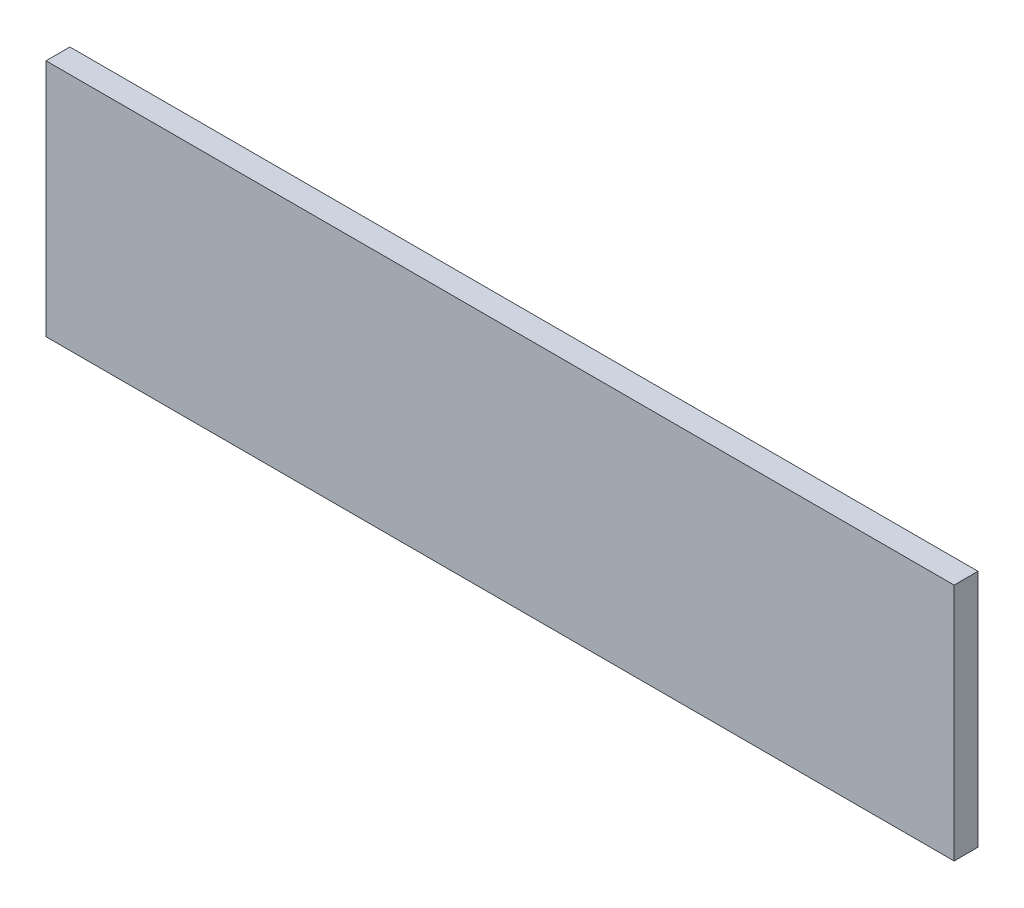
SolidWorks part; units mm, degrees
ref_plane "Front Plane" through (0, 0, 0) normal (0, 0, 1) x (1, 0, 0)
ref_plane "Top Plane" through (0, 0, 0) normal (0, 1, 0) x (1, 0, 0)
ref_plane "Right Plane" through (0, 0, 0) normal (1, 0, 0) x (0, 0, -1)
sketch "Sketch1" plane through (0, 0, 0) normal (0, 0, 1) x (1, 0, 0)
  line L1 (-241.3, -63.5) -> (241.3, -63.5)
  line L2 (-241.3, -63.5) -> (-241.3, 63.5)
  line L3 (-241.3, 63.5) -> (241.3, 63.5)
  line L4 (241.3, -63.5) -> (241.3, 63.5)
  line L5 (-241.3, -63.5) -> (241.3, 63.5) construction
  line L6 (-241.3, 63.5) -> (241.3, -63.5) construction
  point P0 (0, 0)
  dimension "D1" = 127
  dimension "D2" = 482.6
extrude "Boss-Extrude1" add sketch "Sketch1" along normal blind 12.7
